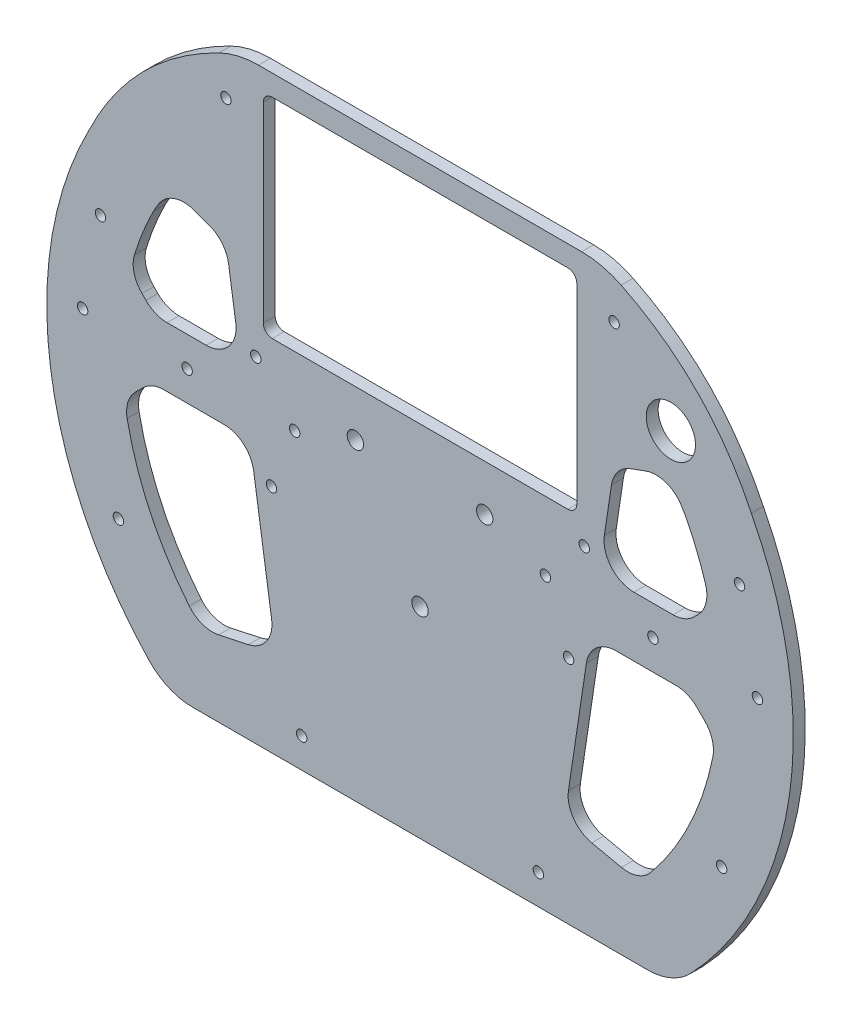
SolidWorks part; units mm, degrees
material "Thornel Mat VMA"
ref_plane "正面" through (0, 0, 0) normal (0, 0, 1) x (1, 0, 0)
ref_plane "平面" through (0, 0, 0) normal (0, 1, 0) x (1, 0, 0)
ref_plane "右側面" through (0, 0, 0) normal (1, 0, 0) x (0, 0, -1)
sketch "ｽｹｯﾁ1" plane through (0, 0, 0) normal (0, 0, 1) x (1, 0, 0)
  line L1 (125, 105) -> (-125, 105) construction
  line L2 (125, 105) -> (125, -105) construction
  line L3 (125, -105) -> (-125, -105) construction
  line L4 (-125, 105) -> (-125, -105) construction
  line L5 (125, 105) -> (-125, -105) construction
  line L6 (125, -105) -> (-125, 105) construction
  circle A0 centre (0, 0) radius 125 construction
  point P0 (0, 0)
  dimension "D3" = 250
  dimension "D1" = 250
  dimension "D2" = 210
ref_plane "平面1" through (0, 0, 0) normal (0, 0, 1) x (1, 0, 0)
sketch "ｽｹｯﾁ2" plane through (0, 0, 0) normal (0, 0, 1) x (1, 0, 0)
  line L0 (0, 45) -> (-38.9711, -22.5) construction
  line L1 (-38.9711, -22.5) -> (38.9711, -22.5) construction
  line L2 (38.9711, -22.5) -> (0, 45) construction
  line L3 (-21.6506, 12.5) -> (21.6506, 12.5) construction
  line L4 (21.6506, 12.5) -> (0, -25) construction
  line L5 (0, -25) -> (-21.6506, 12.5) construction
  circle A0 centre (0, 0) radius 45 construction
  circle A1 centre (0, 0) radius 30 construction
  circle A2 centre (0, 0) radius 25 construction
  arc A3 (-29.9898, -0.784) -> (-15.6738, -25.5799) centre (-38.9711, -22.5) cw construction
  arc A4 (15.6738, -25.5799) -> (29.9898, -0.784) centre (38.9711, -22.5) cw construction
  arc A5 (-14.3159, 26.3639) -> (14.3159, 26.3639) centre (0, 45) ccw construction
  circle A6 centre (-21.6506, 12.5) radius 2.1 construction
  circle A7 centre (21.6506, 12.5) radius 2.1 construction
  circle A8 centre (0, -25) radius 2.1 construction
  dimension "D1" = 90
  dimension "D2" = 60
  dimension "D3" = 50
  dimension "D4" = 23.5
  dimension "D5" = 23.5
  dimension "D6" = 23.5
  dimension "D7" = 4.2
  dimension "D8" = 4.2
  dimension "D9" = 4.2
sketch "ｽｹｯﾁ3" plane through (0, 0, 0) normal (0, 0, 1) x (1, 0, 0)
  line L0 (-125, 105) -> (-125, -105) construction
  line L1 (125, 105) -> (125, -105) construction
  line L2 (-114.5644, 50) -> (114.5644, 50) construction
  line L3 (-105, -100) -> (-75, -100) construction
  line L4 (125, -105) -> (-125, -105) construction
  line L5 (0, 105) -> (0, -105) construction
  line L6 (125, 105) -> (-125, 105) construction
  line L7 (105, -100) -> (75, -100) construction
  arc A0 (-114.5644, 50) -> (-125, 0) centre (0, 0) ccw construction
  circle A1 centre (0, 0) radius 125 construction
  arc A2 (114.5644, 50) -> (125, 0) centre (0, 0) cw construction
  arc A3 (-95, 0) -> (-80.7775, 50) centre (0, 0) cw construction
  arc A4 (114.5644, 50) -> (125, 0) centre (0, 0) cw construction
  arc A5 (95, 0) -> (80.7775, 50) centre (0, 0) ccw construction
  spline S0 degree 3 poles (-125, 0) (-125, -34.2165) (-117.8201, -68.3401) (-105, -100) knots 0 0 0 0 1 1 1 1 construction
  spline S1 degree 3 poles (-75, -100) (-87.8201, -67.9365) (-95, -34.605) (-95, 0) knots 0 0 0 0 1 1 1 1 construction
  spline S2 degree 3 poles (125, 0) (125, -34.2165) (117.8201, -68.3401) (105, -100) knots 0 0 0 0 1 1 1 1 construction
  spline S3 degree 3 poles (75, -100) (87.8201, -67.9365) (95, -34.605) (95, 0) knots 0 0 0 0 1 1 1 1 construction
  point P12 (-120, -50)
  point P13 (-105, -100)
  point P18 (-90, -50)
  point P20 (-95, 0)
  dimension "D1" = 50
  dimension "D2" = 100
  dimension "D9" = 50
  dimension "D3" = 50
  dimension "D4" = 20
  dimension "D5" = 5
  dimension "D6" = 30
  dimension "D7" = 30
  dimension "D8" = 30
  dimension "D10" = 105
sketch "ｽｹｯﾁ4" plane through (0, 0, 0) normal (0, 0, 1) x (1, 0, 0)
  line L5 (125, -105) -> (-125, -105) construction
  line L8 (0, 105) -> (0, -105) construction
  line L10 (-125, 0) -> (125, 0) construction
  line L19 (0, -105) -> (0, 105) construction
  circle A0 centre (0, 0) radius 30 construction
  spline S2 degree 3 poles (-105, -100) (-71.8006, -85.9254) (0, -74.0746) (71.8006, -85.9254) (105, -100) knots 0 0 0 0 0.5 1 1 1 1 construction
  point P21 (-55, -85)
  point P22 (0, -80)
  point P23 (55, -85)
  point P58 (0, 30)
  dimension "D7" = 25
  dimension "D8" = 20
  dimension "D9" = 20
  dimension "D10" = 55
  dimension "D11" = 55
sketch "ｽｹｯﾁ5" plane through (0, 0, 0) normal (0, 0, 1) x (1, 0, 0)
  line L0 (-14.3159, 26.3639) -> (14.3159, 26.3639) construction
  circle A0 centre (0, 0) radius 100 construction
  dimension "D1" = 200
sketch "ｽｹｯﾁ6" plane through (0, 0, 0) normal (0, 0, 1) x (1, 0, 0)
  line L0 (0, -105) -> (0, 105) construction
  line L1 (-52.5, 98) -> (52.5, 98) construction
  line L2 (-52.5, 98) -> (-52.5, 28) construction
  line L3 (-52.5, 28) -> (52.5, 28) construction
  line L4 (52.5, 98) -> (52.5, 28) construction
  line L5 (-52.5, 98) -> (52.5, 28) construction
  line L6 (-52.5, 28) -> (52.5, 98) construction
  line L7 (125, 105) -> (-125, 105) construction
  point P0 (0, 63)
  dimension "D1" = 70
  dimension "D2" = 105
  dimension "D3" = 7
sketch "ｽｹｯﾁ7" plane through (0, 0, 0) normal (0, 0, 1) x (1, 0, 0)
  line L0 (-100, 0) -> (-60, 0) construction
  line L1 (-125, 0) -> (125, 0) construction
  line L2 (-98.8686, 15) -> (-60, 15) construction
  line L3 (-60, 15) -> (-65, 48.2606) construction
  line L4 (-65, 48.2606) -> (-83.5165, 55) construction
  line L5 (-60, 15) -> (-41.9606, -105) construction
  line L6 (125, -105) -> (-125, -105) construction
  line L7 (-60, -5) -> (-56.9934, -5) construction
  line L8 (-125, 105) -> (-125, -105) construction
  line L9 (-83.5165, 55) -> (-89.3029, 45) construction
  line L10 (-89.3029, 45) -> (-110.9703, 57.5377) construction
  line L11 (-110.9703, 57.5377) -> (-92.9863, 83.5377) construction
  line L12 (-92.9863, 83.5377) -> (-60.5, 105) construction
  line L13 (125, 105) -> (-125, 105) construction
  line L14 (-73.1949, -68.1359) -> (-48.3047, -62.7982) construction
  line L15 (-99.8749, -5) -> (-60, -5) construction
  line L16 (0, 0) -> (0, -30) construction
  line L17 (0, -105) -> (0, 105) construction
  line L18 (73.1949, -68.1359) -> (48.3047, -62.7982) construction
  line L19 (60, 15) -> (41.9606, -105) construction
  line L20 (60, -5) -> (56.9934, -5) construction
  line L21 (99.8749, -5) -> (60, -5) construction
  line L22 (98.8686, 15) -> (60, 15) construction
  line L23 (60, 15) -> (65, 48.2606) construction
  line L24 (65, 48.2606) -> (83.5165, 55) construction
  line L25 (83.5165, 55) -> (89.3029, 45) construction
  line L26 (89.3029, 45) -> (110.9703, 57.5377) construction
  line L27 (110.9703, 57.5377) -> (92.9863, 83.5377) construction
  line L28 (92.9863, 83.5377) -> (60.5, 105) construction
  line L29 (47.5613, -67.7434) -> (69.1289, -72.2578) construction
  line L30 (-69.1289, -72.2578) -> (-47.5613, -67.7434) construction
  circle A0 centre (0, 0) radius 100 construction
  circle A1 centre (0, 0) radius 125 construction
  arc A2 (-105, -100) -> (105, -100) centre (0, -348.7469) cw construction
  circle A3 centre (0, -348.7469) radius 270 construction
  circle A4 centre (0, -433.417) radius 132.7909 construction
  circle A5 centre (0, -348.7469) radius 290 construction
  circle A6 centre (0, 0) radius 30 construction
  circle A7 centre (0, -348.7469) radius 285 construction
  spline S0 degree 3 poles (-105, -100) (-71.8006, -85.9254) (0, -74.0746) (71.8006, -85.9254) (105, -100) knots 0 0 0 0 0.5 1 1 1 1 construction
  dimension "D12" = 540
  dimension "D13" = 580
  dimension "D14" = 570
  dimension "D1" = 40
  dimension "D2" = 15
  dimension "D3" = 40
  dimension "D4" = 40
  dimension "D5" = 20
  dimension "D6" = 60
  dimension "D7" = 10
  dimension "D8" = 26
  dimension "D9" = 8
  dimension "D10" = 5
  dimension "D11" = 40
sketch "ｽｹｯﾁ8" plane through (0, 0, 0) normal (0, 0, 1) x (1, 0, 0)
  line L0 (-110.9703, 57.5377) -> (-92.9863, 83.5377)
  line L1 (-92.9863, 83.5377) -> (-60.5, 105)
  line L2 (-60.5, 105) -> (60.5, 105)
  line L3 (60.5, 105) -> (92.9863, 83.5377)
  line L4 (92.9863, 83.5377) -> (110.9703, 57.5377)
  line L5 (-89.3029, 45) -> (-83.5165, 55)
  line L6 (-83.5165, 55) -> (-65, 48.2606)
  line L7 (-65, 48.2606) -> (-60, 15)
  line L8 (-73.1949, -68.1359) -> (-48.3047, -62.7982) construction
  line L9 (89.3029, 45) -> (83.5165, 55)
  line L10 (83.5165, 55) -> (65, 48.2606)
  line L13 (-84.3413, -92.258) -> (84.3413, -92.258)
  line L14 (-56.9934, -5) -> (-48.3047, -62.7982)
  line L15 (65, 48.2606) -> (60, 15)
  line L18 (56.9934, -5) -> (48.3047, -62.7982)
  line L24 (48.3047, -62.7982) -> (73.1949, -68.1359)
  line L25 (73.1949, -68.1359) -> (48.3047, -62.7982) construction
  line L30 (60, 15) -> (98.8686, 15)
  line L31 (56.9934, -5) -> (99.8749, -5)
  line L32 (125, -105) -> (-125, 105) construction
  line L33 (0, 0) -> (0, -30) construction
  line L34 (-60, 15) -> (-98.8686, 15)
  line L35 (-65, 48.2606) -> (-60, 15)
  line L36 (-83.5165, 55) -> (-65, 48.2606)
  line L37 (-89.3029, 45) -> (-83.5165, 55)
  line L38 (-56.9934, -5) -> (-48.3047, -62.7982)
  line L39 (-48.3047, -62.7982) -> (-73.1949, -68.1359)
  line L40 (-56.9934, -5) -> (-99.8749, -5)
  line L41 (-99.8749, -5) -> (-56.9934, -5)
  circle A2 centre (0, -348.7469) radius 290 construction
  arc A5 (98.8686, 15) -> (89.3029, 45) centre (0, 0) ccw
  arc A7 (110.9703, 57.5377) -> (84.3413, -92.258) centre (0, 0) cw
  arc A8 (73.1949, -68.1359) -> (99.8749, -5) centre (0, 0) ccw
  circle A9 centre (0, 0) radius 125 construction
  arc A10 (105, -100) -> (-105, -100) centre (0, -348.7469) ccw construction
  arc A12 (-110.9703, 57.5377) -> (-84.3413, -92.258) centre (0, 0) ccw
  arc A13 (-98.8686, 15) -> (-89.3029, 45) centre (0, 0) cw
  arc A14 (-73.1949, -68.1359) -> (-99.8749, -5) centre (0, 0) cw
extrude "ﾎﾞｽ - 押し出し1" add sketch "ｽｹｯﾁ8" against normal blind 4
sketch "ｽｹｯﾁ9" plane through (0, 0, 0) normal (0, 0, 1) x (1, 0, 0)
  line L0 (-88.8686, 15) -> (-98.8686, 15) construction
  line L1 (-98.8686, 15) -> (-60, 15) construction
  line L2 (-98.8686, 15) -> (-98.8686, 25) construction
  line L3 (-98.8686, 25) -> (-88.8686, 15) construction
  line L4 (-99.8749, -5) -> (-89.8749, -5) construction
  line L5 (-99.8749, -5) -> (-60, -5) construction
  line L6 (-89.8749, -5) -> (-99.8749, -15) construction
  line L7 (-99.8749, -15) -> (-99.8749, -5) construction
  line L8 (0, 0) -> (0, -15) construction
  line L9 (0, -105) -> (0, 105) construction
  line L10 (99.8749, -5) -> (89.8749, -5) construction
  line L11 (89.8749, -5) -> (99.8749, -15) construction
  line L12 (99.8749, -15) -> (99.8749, -5) construction
  line L13 (98.8686, 15) -> (98.8686, 25) construction
  line L14 (98.8686, 25) -> (88.8686, 15) construction
  line L15 (88.8686, 15) -> (98.8686, 15) construction
  dimension "D1" = 10
  dimension "D2" = 10
  dimension "D3" = 10
  dimension "D4" = 10
sketch "ｽｹｯﾁ10" plane through (0, 0, 0) normal (0, 0, 1) x (1, 0, 0)
  line L0 (-99.8749, -15) -> (-89.8749, -5)
  line L1 (-89.8749, -5) -> (-99.8749, -5)
  line L2 (-99.8749, -5) -> (-99.8749, -15)
  line L3 (-98.8686, 15) -> (-88.8686, 15)
  line L4 (-88.8686, 15) -> (-98.8686, 25)
  line L5 (-98.8686, 25) -> (-98.8686, 15)
  line L6 (88.8686, 15) -> (98.8686, 15)
  line L7 (98.8686, 15) -> (98.8686, 25)
  line L8 (98.8686, 25) -> (88.8686, 15)
  line L9 (89.8749, -5) -> (99.8749, -5)
  line L10 (99.8749, -5) -> (99.8749, -15)
  line L11 (99.8749, -15) -> (89.8749, -5)
extrude "ﾎﾞｽ - 押し出し3" add sketch "ｽｹｯﾁ10" against normal blind 4
fillet "ﾌｨﾚｯﾄ1" radius 10 12 edges at (-48.3047, -62.7982, -2) (48.3047, -62.7982, -2) (73.1949, -68.1359, -2) (-73.1949, -68.1359, -2) (98.9977, -14.1228, -2) (89.8749, -5, -2) (88.8686, 15, -2) (97.2324, 23.3638, -2) (-89.8749, -5, -2) (-98.9977, -14.1228, -2) (-88.8686, 15, -2) (-97.2324, 23.3638, -2)
fillet "ﾌｨﾚｯﾄ2" radius 10 4 edges at (60, 15, -2) (-60, 15, -2) (56.9934, -5, -2) (-56.9934, -5, -2)
fillet "ﾌｨﾚｯﾄ3" radius 10 4 edges at (-83.5165, 55, -2) (-65, 48.2606, -2) (65, 48.2606, -2) (83.5165, 55, -2)
fillet "ﾌｨﾚｯﾄ4" radius 20 2 edges at (84.3413, -92.258, -2) (-84.3413, -92.258, -2)
sketch "ｽｹｯﾁ11" plane through (0, 0, 0) normal (0, 0, 1) x (1, 0, 0)
  line L1 (-52.5, 98) -> (52.5, 98)
  line L2 (-52.5, 98) -> (-52.5, 28)
  line L3 (-52.5, 28) -> (52.5, 28)
  line L4 (52.5, 98) -> (52.5, 28)
  line L5 (-52.5, 98) -> (52.5, 28) construction
  line L6 (-52.5, 28) -> (52.5, 98) construction
  point P0 (0, 63)
  dimension "D1" = 70
  dimension "D2" = 105
extrude "ｶｯﾄ - 押し出し1" cut sketch "ｽｹｯﾁ11" against normal blind 10
fillet "ﾌｨﾚｯﾄ7" radius 3 4 edges at (52.5, 98, -2) (52.5, 28, -2) (-52.5, 98, -2) (-52.5, 28, -2)
sketch "ｽｹｯﾁ12" plane through (0, 0, 0) normal (0, 0, 1) x (1, 0, 0)
  line L2 (-110.9703, 57.5377) -> (-92.9863, 83.5377)
  line L3 (-92.9863, 83.5377) -> (-60.5, 105)
  line L4 (60.5, 105) -> (92.9863, 83.5377)
  line L5 (92.9863, 83.5377) -> (110.9703, 57.5377)
  circle A0 centre (0, 0) radius 125 construction
  spline S0 degree 2 poles (-110.9703, 57.5377) (-95.1002, 90.8355) (-60.5, 105) knots 0 0 0 1 1 1
  spline S1 degree 2 poles (110.9703, 57.5377) (95.1002, 90.8355) (60.5, 105) knots 0 0 0 1 1 1
extrude "ﾎﾞｽ - 押し出し4" add sketch "ｽｹｯﾁ12" against normal blind 4 contours S0 L3 | S0 L2 | L4 S1 | L5 S1
fillet "ﾌｨﾚｯﾄ8" radius 30 2 edges at (60.5, 105, -2) (-60.5, 105, -2)
sketch "ｽｹｯﾁ13" plane through (0, 0, 0) normal (0, 0, 1) x (1, 0, 0)
  line L0 (0, 0) -> (0, -25) construction
  line L1 (65.6025, -5) -> (85.7328, -5) construction
  line L2 (125, 105) -> (125, -105) construction
  line L3 (-125, 0) -> (125, 0) construction
  circle A0 centre (107, 35) radius 1.75
  circle A1 centre (113, 5) radius 1.75
  circle A2 centre (78, 5) radius 1.75
  circle A3 centre (101, -50) radius 1.75
  circle A4 centre (-101, -50) radius 1.75
  circle A5 centre (-78, 5) radius 1.75
  circle A6 centre (-113, 5) radius 1.75
  circle A7 centre (-107, 35) radius 1.75
  dimension "D1" = 3.5
  dimension "D2" = 3.5
  dimension "D3" = 3.5
  dimension "D4" = 3.5
  dimension "D5" = 10
  dimension "D6" = 10
  dimension "D7" = 12
  dimension "D8" = 47
  dimension "D9" = 50
  dimension "D10" = 24
  dimension "D11" = 35
  dimension "D12" = 18
extrude "ｶｯﾄ - 押し出し2" cut sketch "ｽｹｯﾁ13" against normal blind 10
sketch "ｽｹｯﾁ14" plane through (0, 0, 0) normal (0, 0, 1) x (1, 0, 0)
  line L0 (0, -105) -> (0, 105) construction
  line L1 (125, 105) -> (-125, 105) construction
  line L2 (-125, 0) -> (125, 0) construction
  line L3 (-55.7136, -13.5134) -> (-49.7018, -53.5045) construction
  line L4 (-55, 20) -> (-36.209, -105) construction
  line L5 (125, -105) -> (-125, -105) construction
  line L6 (-76.1826, -92.258) -> (76.1826, -92.258) construction
  line L7 (0, -15) -> (0, -45) construction
  circle A0 centre (-65, 90) radius 1.75
  circle A1 centre (-55, 20) radius 1.75
  circle A2 centre (-49.7385, -15) radius 1.75
  circle A3 centre (-39.6277, -82.258) radius 1.75
  circle A4 centre (0, 0) radius 45 construction
  circle A5 centre (65, 90) radius 1.75
  circle A6 centre (55, 20) radius 1.75
  circle A7 centre (49.7385, -15) radius 1.75
  circle A8 centre (39.6277, -82.258) radius 1.75
  dimension "D1" = 3.5
  dimension "D2" = 65
  dimension "D3" = 15
  dimension "D4" = 3.5
  dimension "D5" = 55
  dimension "D6" = 20
  dimension "D7" = 3.5
  dimension "D8" = 15
  dimension "D9" = 3.5
  dimension "D10" = 10
extrude "ｶｯﾄ - 押し出し3" cut sketch "ｽｹｯﾁ14" against normal blind 10
sketch "ｽｹｯﾁ15" plane through (0, 0, 0) normal (0, 0, 1) x (1, 0, 0)
  circle A0 centre (-21.6506, 12.5) radius 2.75
  circle A1 centre (21.6506, 12.5) radius 2.75
  circle A2 centre (0, -25) radius 2.75
  dimension "D1" = 5.5
  dimension "D2" = 5.5
  dimension "D3" = 5.5
extrude "ｶｯﾄ - 押し出し4" cut sketch "ｽｹｯﾁ15" against normal blind 10
sketch "ｽｹｯﾁ16" plane through (0, 0, 0) normal (0, 0, 1) x (1, 0, 0)
  line L0 (0, -105) -> (0, 105) construction
  line L1 (-125, 0) -> (125, 0) construction
  circle A0 centre (84, 68) radius 8.25
  dimension "D1" = 84
  dimension "D2" = 68
  dimension "D3" = 16.5
extrude "ｶｯﾄ - 押し出し5" cut sketch "ｽｹｯﾁ16" against normal blind 10
sketch "ｽｹｯﾁ17" plane through (0, 0, 0) normal (0, 0, 1) x (1, 0, 0)
  line L0 (0, -105) -> (0, 105) construction
  line L1 (-125, 0) -> (125, 0) construction
  circle A0 centre (-84, 68) radius 8.25
  dimension "D1" = 16.5
  dimension "D2" = 84
  dimension "D3" = 68
sketch "ｽｹｯﾁ18" plane through (0, 0, 0) normal (0, 0, 1) x (1, 0, 0)
  line L0 (-125, 0) -> (125, 0) construction
  line L1 (0, 0) -> (0, -33) construction
  circle A0 centre (0, 0) radius 33 construction
  circle A1 centre (-42, 5) radius 1.75
  circle A2 centre (42, 5) radius 1.75
  point P3 (-33, 0)
  point P4 (-42, 0)
  dimension "D1" = 66
  dimension "D3" = 3.5
  dimension "D2" = 9
  dimension "D4" = 5
extrude "ｶｯﾄ - 押し出し6" cut sketch "ｽｹｯﾁ18" against normal blind 10
